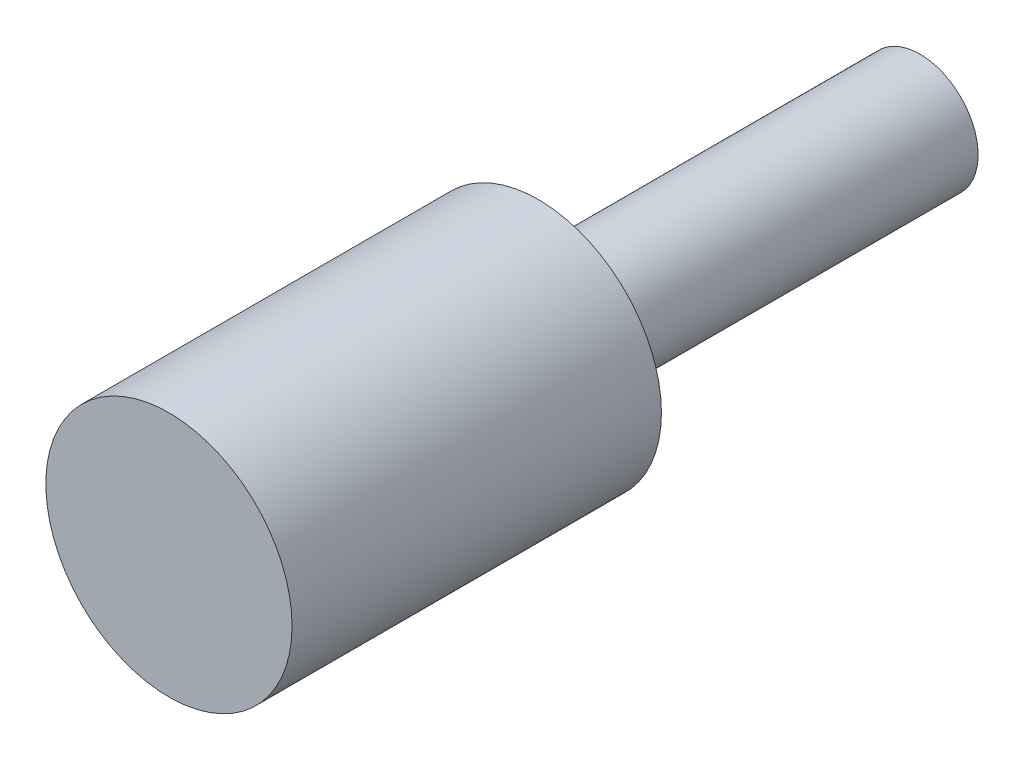
SolidWorks part; units mm, degrees
ref_plane "Front Plane" through (0, 0, 0) normal (0, 0, 1) x (1, 0, 0)
ref_plane "Top Plane" through (0, 0, 0) normal (0, 1, 0) x (1, 0, 0)
ref_plane "Right Plane" through (0, 0, 0) normal (1, 0, 0) x (0, 0, -1)
sketch "Sketch1" plane through (0, 0, 0) normal (0, 0, 1) x (1, 0, 0)
  circle A0 centre (0, 0) radius 10
  dimension "D1" = 20
extrude "Boss-Extrude1" add sketch "Sketch1" along normal blind 30
sketch "Sketch2" plane through (0, 0, 0) normal (0, 0, -1) x (-1, 0, 0)
  circle A0 centre (0, 0) radius 4.7208
extrude "Boss-Extrude2" add sketch "Sketch2" along normal blind 31 contours A0
